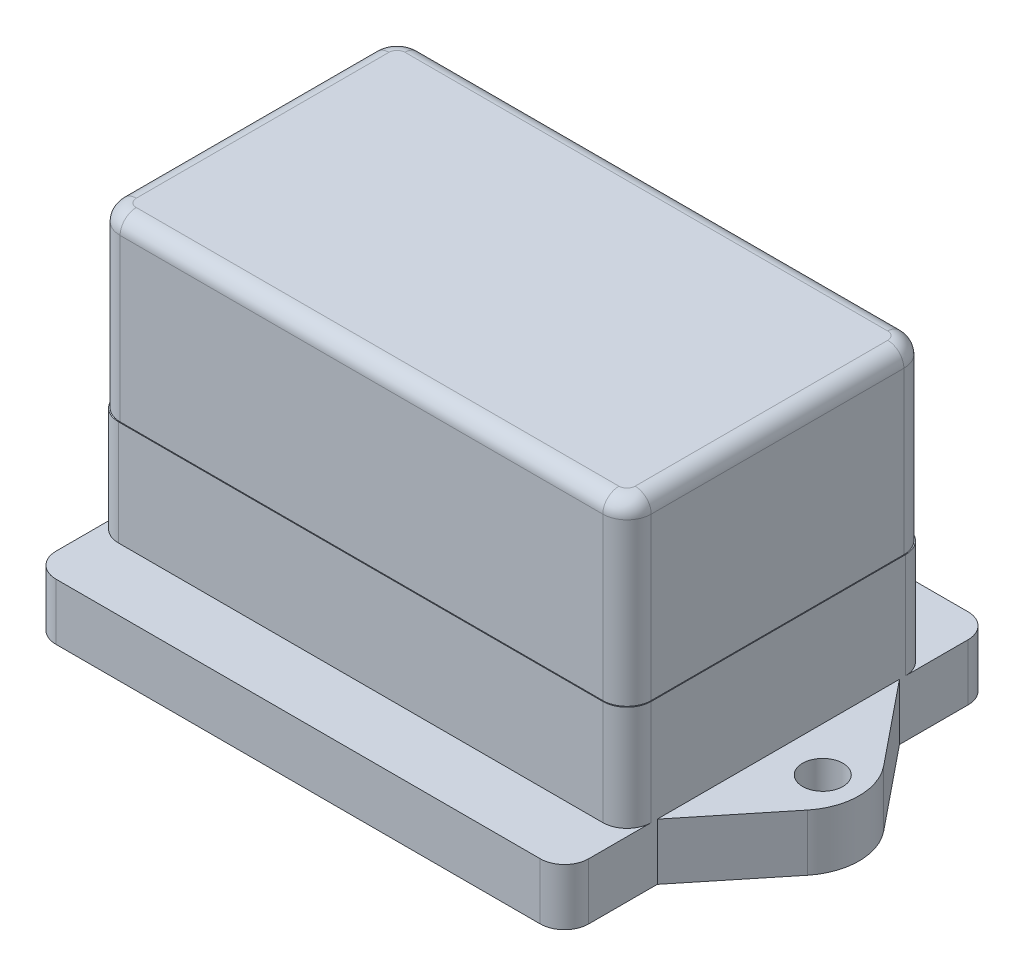
SolidWorks part; units mm, degrees
ref_plane "Front Plane" through (0, 0, 0) normal (0, 0, 1) x (1, 0, 0)
ref_plane "Top Plane" through (0, 0, 0) normal (0, 1, 0) x (1, 0, 0)
ref_plane "Right Plane" through (0, 0, 0) normal (1, 0, 0) x (0, 0, -1)
sketch "Sketch1" plane through (0, 0, 0) normal (0, 1, 0) x (1, 0, 0)
  line L0 (0, -853.2884) -> (0, 41811.1338) construction
  line L1 (-853.2884, 0) -> (41811.1338, 0) construction
  line L2 (-41.3275, 4.7213) -> (-33, 15)
  line L3 (-33, 15) -> (-33, 26.5)
  line L4 (-33, 26.5) -> (33, 26.5)
  line L5 (33, 15) -> (33, 26.5)
  line L6 (41.3275, 4.7213) -> (33, 15)
  line L7 (41.3275, -4.7213) -> (33, -15)
  line L8 (33, -15) -> (33, -26.5)
  line L9 (-33, -26.5) -> (33, -26.5)
  line L10 (-33, -15) -> (-33, -26.5)
  line L11 (-41.3275, -4.7213) -> (-33, -15)
  arc A0 (-41.3275, -4.7213) -> (-41.3275, 4.7213) centre (-35.5, 0) cw
  arc A1 (41.3275, -4.7213) -> (41.3275, 4.7213) centre (35.5, 0) ccw
  point P12 (0, 26.5)
  dimension "D5" = 7.5
  dimension "D1" = 35.5
  dimension "D2" = 26.5
  dimension "D3" = 30
  dimension "D4" = 66
extrude "Boss-Extrude1" add sketch "Sketch1" along normal blind 7
hole_wizard "Ø5.0mm Dowel Hole1" positions "Sketch2" profile "Sketch3" hole size "Ø5.0" standard "DIN" end condition up to next
sketch "Sketch2" plane through (0, 7, 0) normal (0, 1, 0) x (1, 0, 0)
  point P0 (-38.5, 0)
  point P2 (38.5, 0)
  point P6 (0, 0)
  dimension "D1" = 77
  dimension "D2" = 38.5
sketch "Sketch3" plane through (-38.5, 7, 0) normal (1, 0, 0) x (0, 0, 1)
  line L0 (0, 0) -> (0, 7)
  line L1 (0, 7) -> (2.5, 7)
  line L2 (2.5, 7) -> (2.5, 0)
  line L5 (2.5, 0) -> (0, 0)
  line L11 (0, -6.35) -> (0, 107.95) construction
  dimension "Thru Hole Dia." = 5
  dimension "Thru Hole Depth" = 7
sketch "Sketch4" plane through (0, 7, 0) normal (0, 1, 0) x (1, 0, 0)
  line L0 (33, 15) -> (33, 26.5) construction
  line L1 (-33, -18.75) -> (33, -18.75)
  line L2 (-33, -18.75) -> (-33, 18.75)
  line L3 (-33, 18.75) -> (33, 18.75)
  line L4 (33, -18.75) -> (33, 18.75)
  line L5 (-33, -18.75) -> (33, 18.75) construction
  line L6 (-33, 18.75) -> (33, -18.75) construction
  point P0 (0, 0)
  dimension "D1" = 37.5
extrude "Boss-Extrude2" add sketch "Sketch4" along normal blind 13
sketch "Sketch5" plane through (0, 20, 0) normal (0, 1, 0) x (1, 0, 0)
  line L0 (33, -18.75) -> (33, 18.75) construction
  line L1 (-32.9, -18.65) -> (32.9, -18.65)
  line L2 (-32.9, -18.65) -> (-32.9, 18.65)
  line L3 (-32.9, 18.65) -> (32.9, 18.65)
  line L4 (32.9, -18.65) -> (32.9, 18.65)
  line L5 (-32.9, -18.65) -> (32.9, 18.65) construction
  line L6 (-32.9, 18.65) -> (32.9, -18.65) construction
  line L7 (33, 18.75) -> (-33, 18.75) construction
  point P0 (0, 0)
  dimension "D1" = 0.1
  dimension "D2" = 0.1
extrude "Boss-Extrude3" add sketch "Sketch5" along normal blind 22
fillet "Fillet1" radius 3 12 edges at (33, 3.5, -26.5) (-33, 3.5, -26.5) (-33, 3.5, 26.5) (33, 3.5, 26.5) (32.9, 31, 18.65) (33, 13.5, 18.75) (32.9, 31, -18.65) (33, 13.5, -18.75) (-32.9, 31, -18.65) (-32.9, 31, 18.65) (-33, 13.5, -18.75) (-33, 13.5, 18.75)
fillet "Fillet2" radius 2 8 edges at (-32.0213, 42, 17.7713) (-32.9, 42, 0) (-32.0213, 42, -17.7713) (0, 42, -18.65) (32.0213, 42, -17.7713) (32.9, 42, 0) (32.0213, 42, 17.7713) (0, 42, 18.65)
